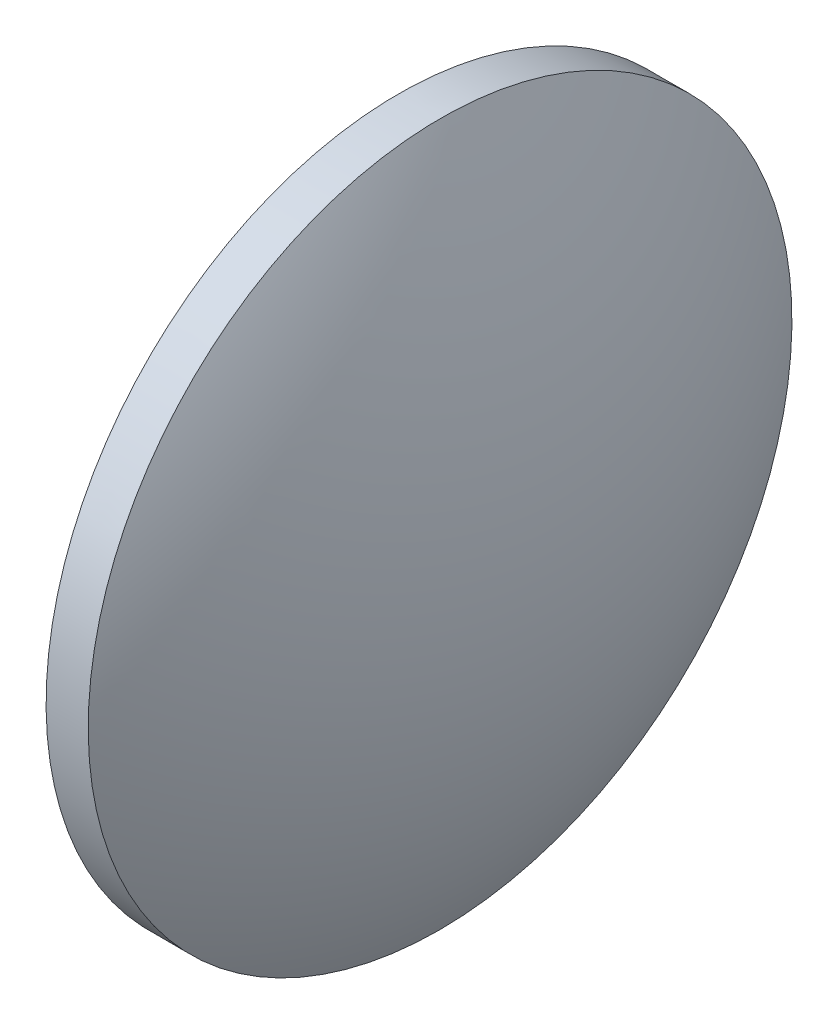
SolidWorks part; units mm, degrees
ref_plane "前视基准面" through (0, 0, 0) normal (0, 0, 1) x (1, 0, 0)
ref_plane "上视基准面" through (0, 0, 0) normal (0, 1, 0) x (1, 0, 0)
ref_plane "右视基准面" through (0, 0, 0) normal (1, 0, 0) x (0, 0, -1)
sketch "草图1" plane through (0, 0, 0) normal (0, 0, 1) x (1, 0, 0)
  line L0 (554.4849, 117.9135) -> (575.6119, 117.8725) construction
  line L1 (559.1328, 117.9045) -> (559.1328, 142.9045)
  line L2 (559.1328, 142.9045) -> (562.1328, 142.9045)
  line L3 (568.5828, 117.8862) -> (559.1328, 117.9045)
  arc A0 (568.5828, 117.8862) -> (562.1328, 142.9045) centre (516.9082, 117.9045) ccw
revolve "旋转1" add sketch "草图1" angle 360 about L0
